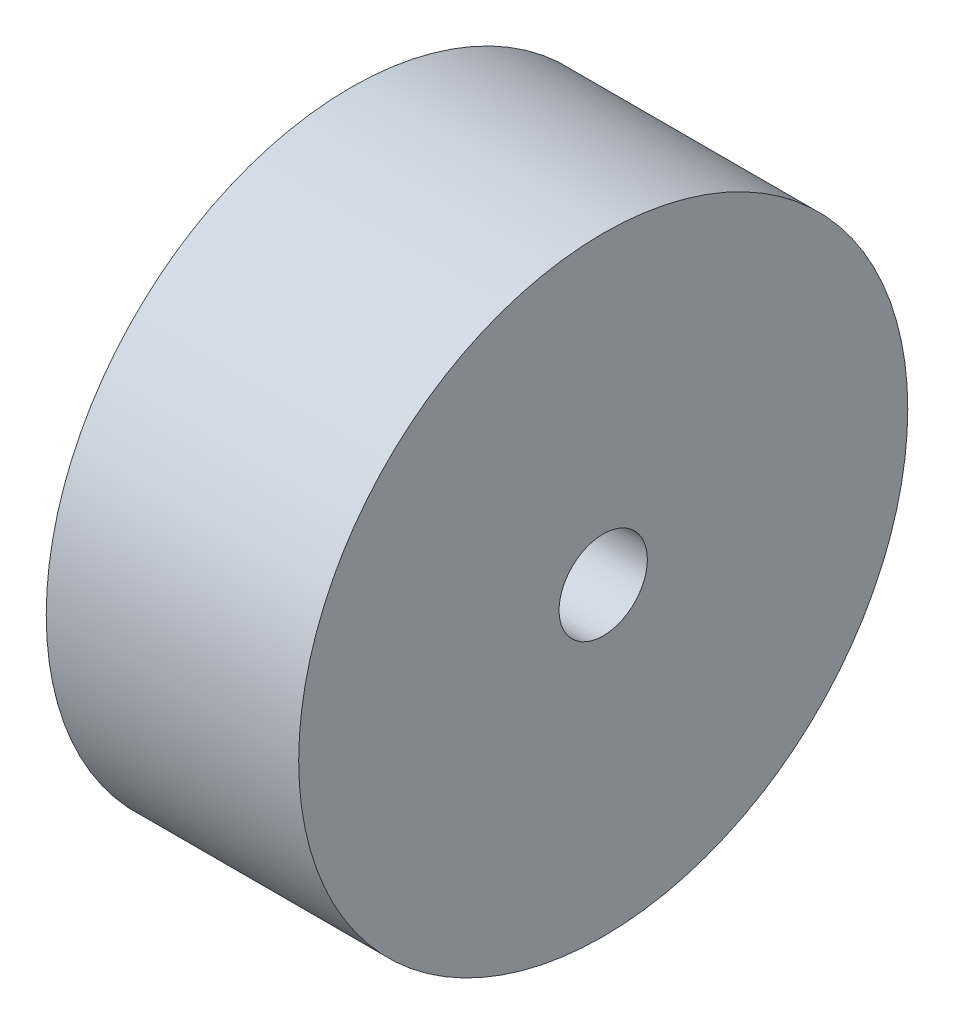
SolidWorks part; units mm, degrees
material "Thornel Mat VMA"
ref_plane "Front Plane" through (0, 0, 0) normal (0, 0, 1) x (1, 0, 0)
ref_plane "Top Plane" through (0, 0, 0) normal (0, 1, 0) x (1, 0, 0)
ref_plane "Right Plane" through (0, 0, 0) normal (1, 0, 0) x (0, 0, -1)
sketch "Sketch1" plane through (0, 0, 0) normal (1, 0, 0) x (0, 0, -1)
  circle A0 centre (0, 0) radius 17.25
  dimension "D1" = 34.5
extrude "Boss-Extrude1" add sketch "Sketch1" along normal blind 14.3 contours A0
sketch "Sketch2" plane through (14.3, 0, 0) normal (1, 0, 0) x (0, 0, -1)
  circle A0 centre (0, 0) radius 2.5
  dimension "D1" = 5
extrude "Cut-Extrude1" cut sketch "Sketch2" against normal through all both and the other way through all
